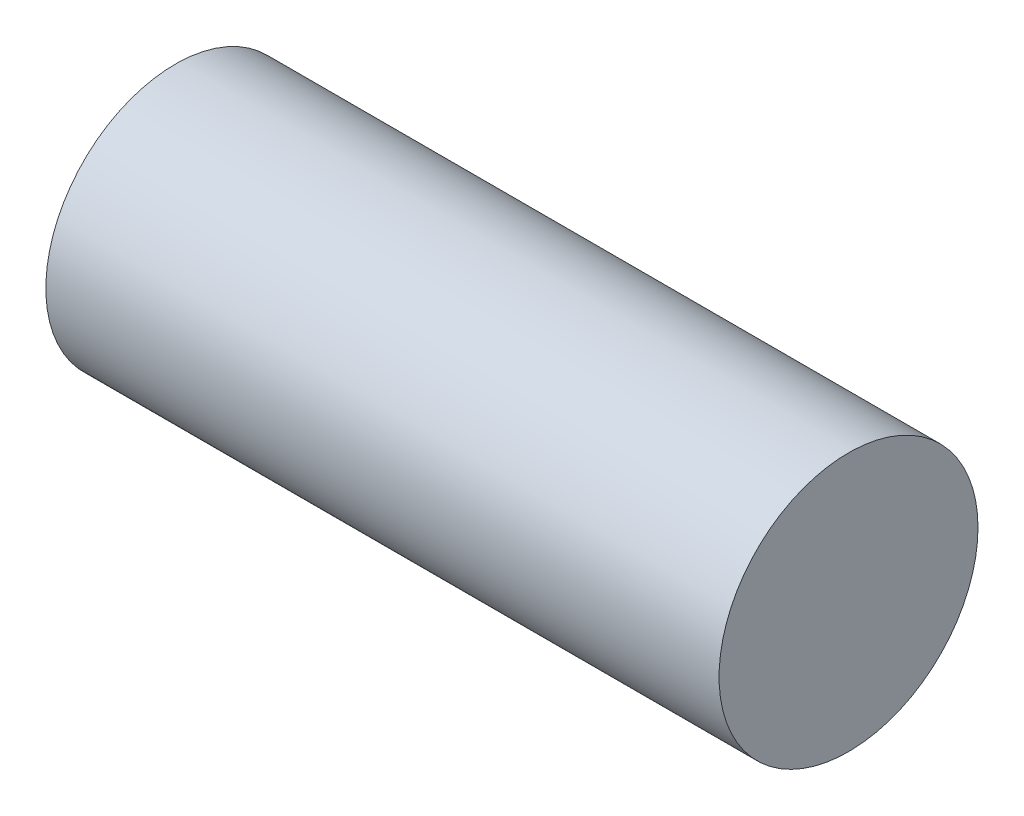
SolidWorks part; units mm, degrees
material "Titanium"
ref_plane "Front Plane" through (0, 0, 0) normal (0, 0, 1) x (1, 0, 0)
ref_plane "Top Plane" through (0, 0, 0) normal (0, 1, 0) x (1, 0, 0)
ref_plane "Right Plane" through (0, 0, 0) normal (1, 0, 0) x (0, 0, -1)
sketch "Sketch1" plane through (0, 0, 0) normal (1, 0, 0) x (0, 0, -1)
  circle A0 centre (0, 0) radius 5
  dimension "D1" = 10
extrude "Extrude1" add sketch "Sketch1" along normal blind 26
